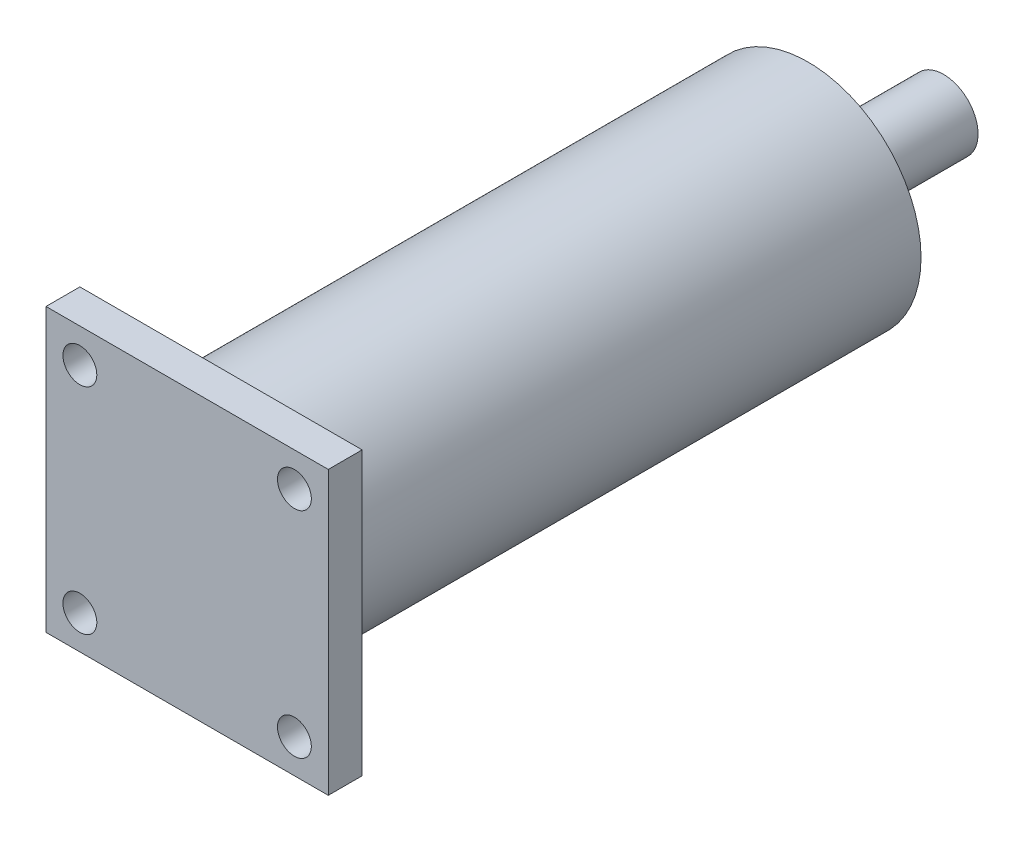
SolidWorks part; units mm, degrees
ref_plane "前视基准面" through (0, 0, 0) normal (0, 0, 1) x (1, 0, 0)
ref_plane "上视基准面" through (0, 0, 0) normal (0, 1, 0) x (1, 0, 0)
ref_plane "右视基准面" through (0, 0, 0) normal (1, 0, 0) x (0, 0, -1)
sketch "草图2" plane through (0, 0, 0) normal (0, 0, 1) x (1, 0, 0)
  line L1 (0, 0) -> (25, 0)
  line L2 (0, 0) -> (0, -25)
  line L3 (0, -25) -> (25, -25)
  line L4 (25, 0) -> (25, -25)
  dimension "D1" = 25
  dimension "D2" = 25
extrude "凸台-拉伸1" add sketch "草图2" along normal blind 3
sketch "草图3" plane through (0, 0, 0) normal (0, 0, -1) x (-1, 0, 0)
  line L0 (-12.5, 0) -> (-12.5, -16.674) construction
  line L1 (-25, 0) -> (0, 0) construction
  line L2 (-25, -12.5) -> (0, -12.5) construction
  line L3 (-25, -25) -> (-25, 0) construction
  line L4 (0, 0) -> (0, -25) construction
  circle A0 centre (-22, -3) radius 1.5
  circle A1 centre (-3, -3) radius 1.5
  circle A2 centre (-3, -22) radius 1.5
  circle A3 centre (-22, -22) radius 1.5
  dimension "D3" = 3
  dimension "D1" = 3
  dimension "D2" = 3
extrude "切除-拉伸2" cut sketch "草图3" against normal through all
sketch "草图4" plane through (0, 0, 3) normal (0, 0, 1) x (1, 0, 0)
  line L0 (0, 0) -> (25, -25) construction
  line L7 (19, -19) -> (6, -6) construction
  circle A0 centre (12.5, -12.5) radius 10
  point P4 (12.5, -12.5)
  dimension "D1" = 20
extrude "凸台-拉伸2" add sketch "草图4" against normal blind 52 from surface at -3 starting at face at (23.5, -22, 0)
sketch "草图5" plane through (0, 0, -52) normal (0, 0, -1) x (-1, 0, 0)
  line L0 (-21.2215, -17.3924) -> (-3.7785, -7.6076) construction
  circle A3 centre (-12.5, -12.5) radius 10 construction
  circle A4 centre (-12.5, -12.5) radius 3.05
  dimension "D1" = 6.1
extrude "凸台-拉伸3" add sketch "草图5" along normal blind 12
